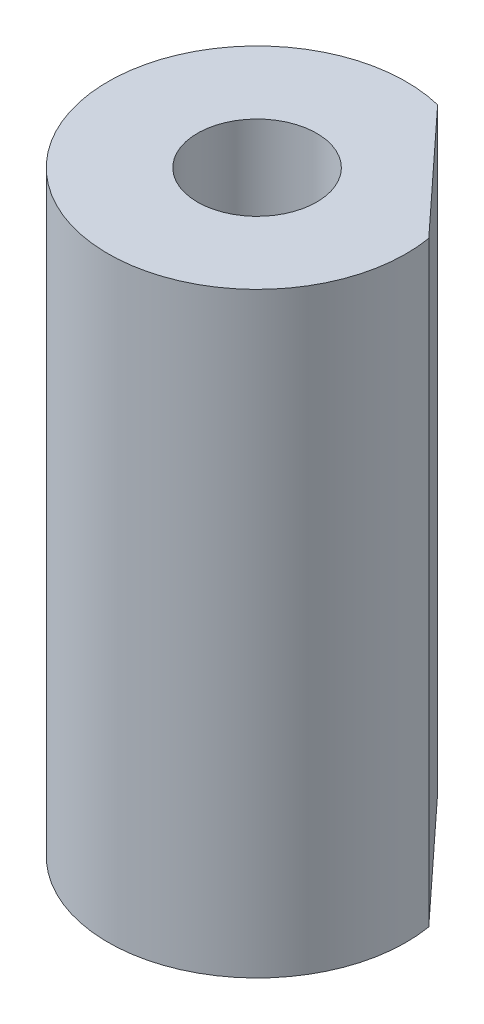
SolidWorks part; units mm, degrees
ref_plane "Front Plane" through (0, 0, 0) normal (0, 0, 1) x (1, 0, 0)
ref_plane "Top Plane" through (0, 0, 0) normal (0, 1, 0) x (1, 0, 0)
ref_plane "Right Plane" through (0, 0, 0) normal (1, 0, 0) x (0, 0, -1)
sketch "Sketch1" plane through (0, 0, 0) normal (0, 1, 0) x (1, 0, 0)
  circle A0 centre (0, 0) radius 12.5
  circle A1 centre (0, 0) radius 5
  dimension "D1" = 10
  dimension "D2" = 25
extrude "Boss-Extrude1" add sketch "Sketch1" along normal blind 50
sketch "Sketch2" plane through (0, 50, 0) normal (0, 1, 0) x (1, 0, 0)
  line L0 (-20.4347, 4.0832) -> (16.4501, 16.7524) construction
  line L1 (3.0035, 12.1338) -> (12.3279, 2.067)
  arc A0 (3.0035, 12.1338) -> (12.3279, 2.067) centre (0, 0) cw
  circle A1 centre (0, 0) radius 12.5 construction
extrude "Cut-Extrude1" cut sketch "Sketch2" against normal through all
